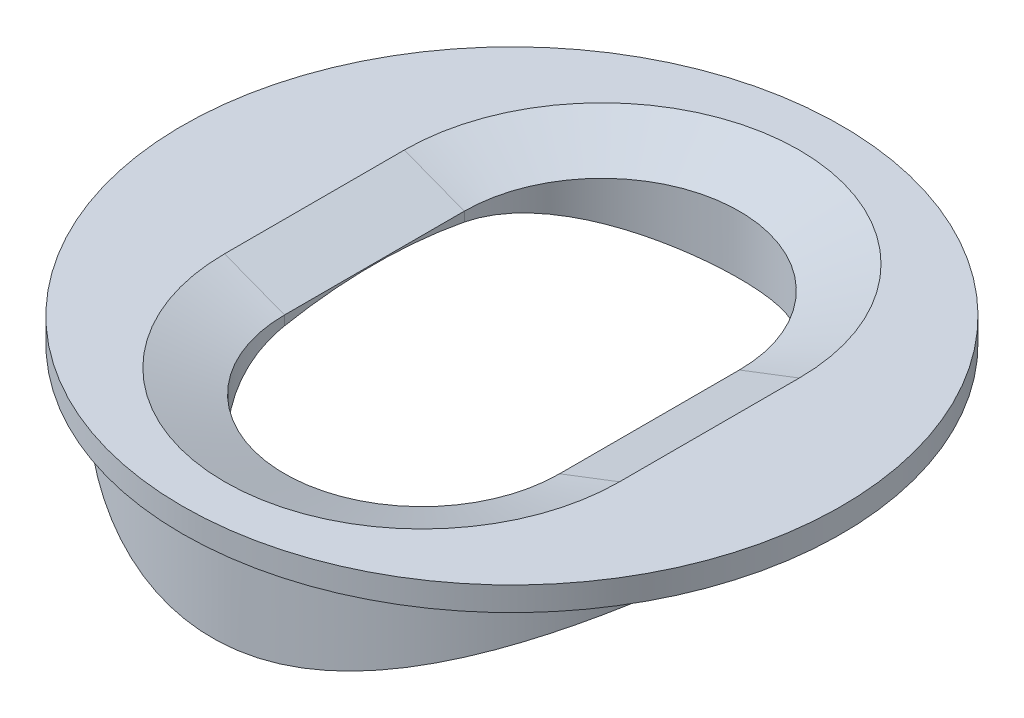
SolidWorks part; units mm, degrees
ref_plane "Front Plane" through (0, 0, 0) normal (0, 0, 1) x (1, 0, 0)
ref_plane "Top Plane" through (0, 0, 0) normal (0, 1, 0) x (1, 0, 0)
ref_plane "Right Plane" through (0, 0, 0) normal (1, 0, 0) x (0, 0, -1)
sketch "Sketch1" plane through (0, 0, 0) normal (0, 1, 0) x (1, 0, 0)
  circle A0 centre (0, 0) radius 5
extrude "Boss-Extrude1" add sketch "Sketch1" along normal blind 5
sketch "Sketch2" plane through (0, 5, 0) normal (0, 1, 0) x (1, 0, 0)
  circle A0 centre (0, 0) radius 5.5
extrude "Boss-Extrude2" add sketch "Sketch2" along normal blind 0.4
sketch "Sketch4" plane through (0, 5.4, 0) normal (0, 1, 0) x (1, 0, 0)
  line L0 (0, 1.5) -> (0, -1.5) construction
  line L1 (2.2953, 1.5) -> (2.2953, -1.5)
  line L2 (-2.2953, 1.5) -> (-2.2953, -1.5)
  arc A0 (2.2953, 1.5) -> (-2.2953, 1.5) centre (0, 1.5) ccw
  arc A1 (-2.2953, -1.5) -> (2.2953, -1.5) centre (0, -1.5) ccw
  point P3 (0, 0)
  dimension "D1" = 1.5
  dimension "D2" = 1.5
extrude "Cut-Extrude1" cut sketch "Sketch4" against normal through all
sketch "Sketch5" plane through (0, 0, 0) normal (1, 0, 0) x (0, 0, -1)
  circle A0 centre (0, -3) radius 8
extrude "Cut-Extrude2" cut sketch "Sketch5" against normal through all and the other way through all
sketch "Sketch6" plane through (0, 5.4, 0) normal (0, 1, 0) x (-1, 0, 0)
  circle A0 centre (0, 0) radius 5
chamfer "Chamfer4" distance 1 angle 21 4 edges at (0, 5.4, -3.7953) (-2.2953, 5.4, 0) (2.2953, 5.4, 0) (0, 5.4, 3.7953)
